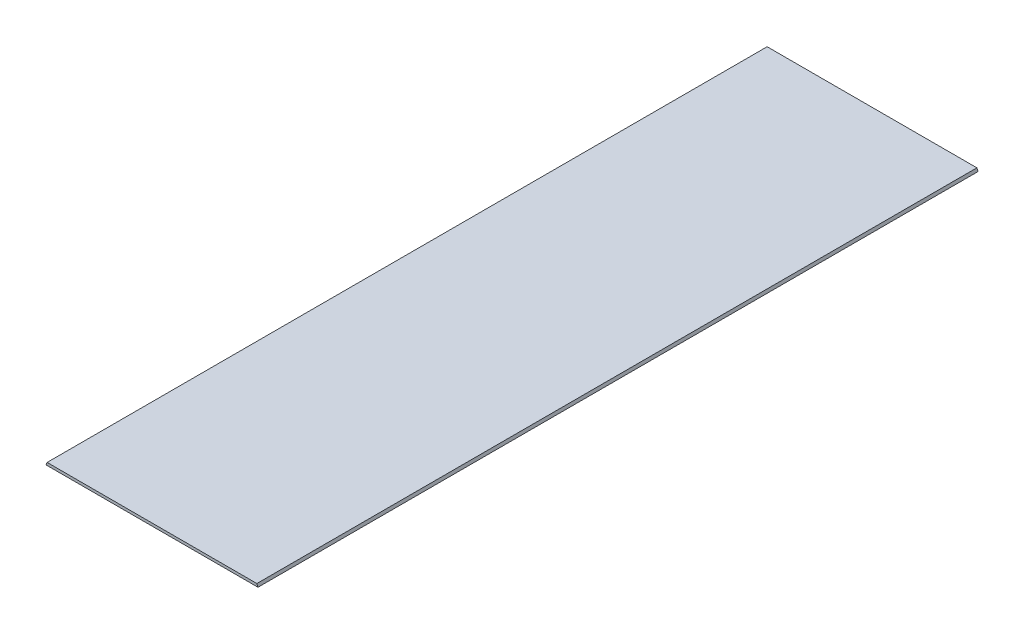
SolidWorks part; units mm, degrees
ref_plane "Front Plane" through (0, 0, 0) normal (0, 0, 1) x (1, 0, 0)
ref_plane "Top Plane" through (0, 0, 0) normal (0, 1, 0) x (1, 0, 0)
ref_plane "Right Plane" through (0, 0, 0) normal (1, 0, 0) x (0, 0, -1)
sketch "Sketch1" plane through (0, 0, 0) normal (0, 0, 1) x (1, 0, 0)
  line L0 (0, 0) -> (0.9785, 2.3622)
  line L1 (0.9785, 2.3622) -> (184.1125, 2.3622)
  line L2 (184.1125, 2.3622) -> (185.0909, 0)
  line L3 (185.0909, 0) -> (0, 0)
  dimension "D1" = 2.3622
  dimension "D2" = 67.5
  dimension "D3" = 67.5
  dimension "D4" = 183.134
extrude "Boss-Extrude1" add sketch "Sketch1" along normal blind 628.65
